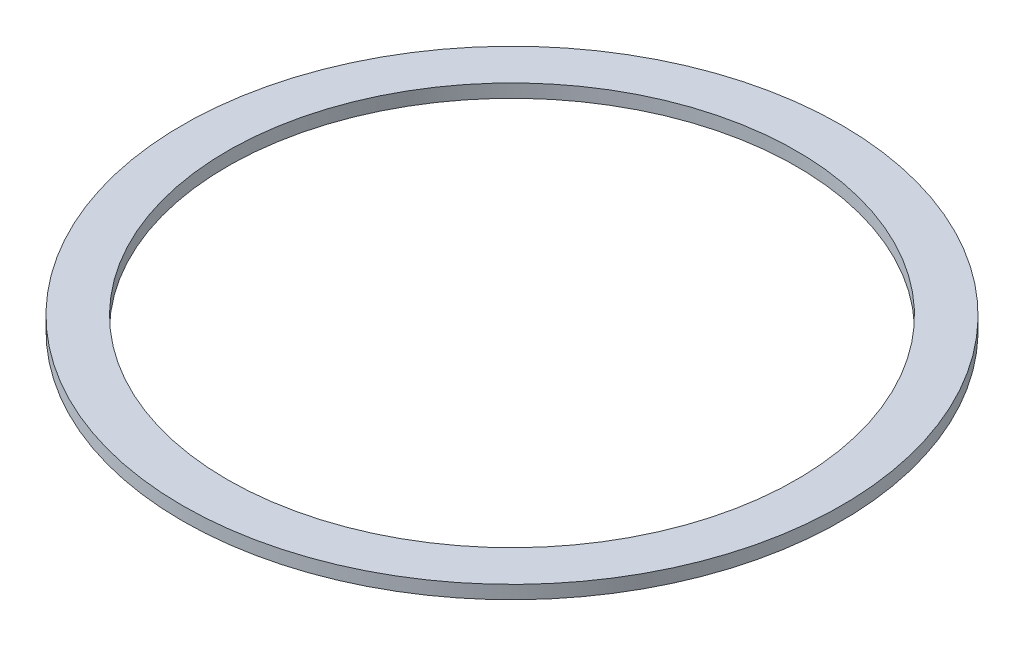
SolidWorks part; units mm, degrees
ref_plane "Plano frontal" through (0, 0, 0) normal (0, 0, 1) x (1, 0, 0)
ref_plane "Plano superior" through (0, 0, 0) normal (0, 1, 0) x (1, 0, 0)
ref_plane "Plano direito" through (0, 0, 0) normal (1, 0, 0) x (0, 0, -1)
sketch "Esboço1" plane through (0, 0, 0) normal (0, 1, 0) x (1, 0, 0)
  circle A0 centre (0, 0) radius 85.5
  circle A1 centre (0, 0) radius 99
extrude "Ressalto-extrusão1" add sketch "Esboço1" along normal blind 4
